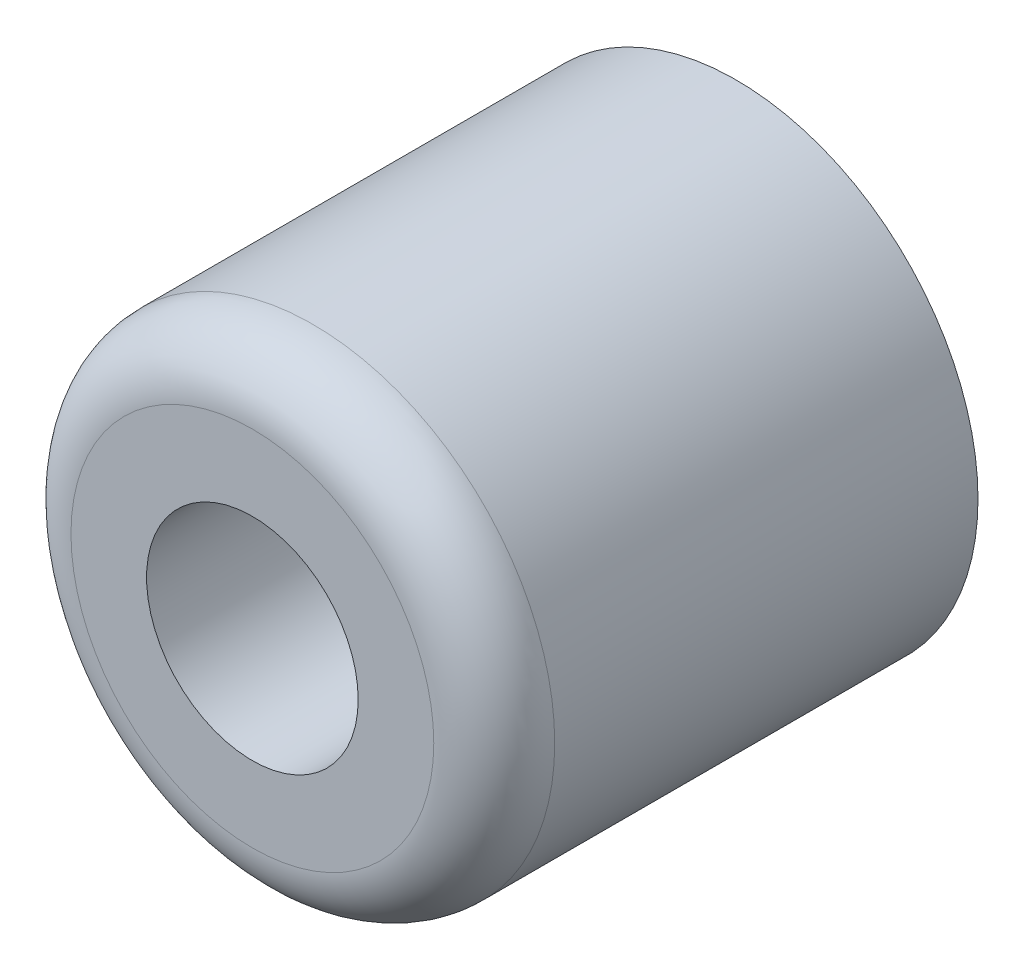
SolidWorks part; units mm, degrees
material "POLYURETHANE (11671)"
ref_plane "Front Plane" through (0, 0, 0) normal (0, 0, 1) x (1, 0, 0)
ref_plane "Top Plane" through (0, 0, 0) normal (0, 1, 0) x (1, 0, 0)
ref_plane "Right Plane" through (0, 0, 0) normal (1, 0, 0) x (0, 0, -1)
sketch "Sketch1" plane through (0, 0, 0) normal (0, 0, 1) x (1, 0, 0)
  circle A0 centre (0, 0) radius 12.7
  circle A1 centre (0, 0) radius 3.5719
  dimension "D1" = 25.4
  dimension "D2" = 7.1437
extrude "Boss-Extrude1" add sketch "Sketch1" along normal blind 25.4
sketch "Sketch2" plane through (0, 0, 25.4) normal (0, 0, 1) x (1, 0, 0)
  circle A0 centre (0, 0) radius 5.5562
  dimension "D1" = 11.1125
extrude "Cut-Extrude1" cut sketch "Sketch2" against normal blind 12.7
fillet "Fillet1" radius 3.175 1 edges at (12.7, 0, 25.4)
